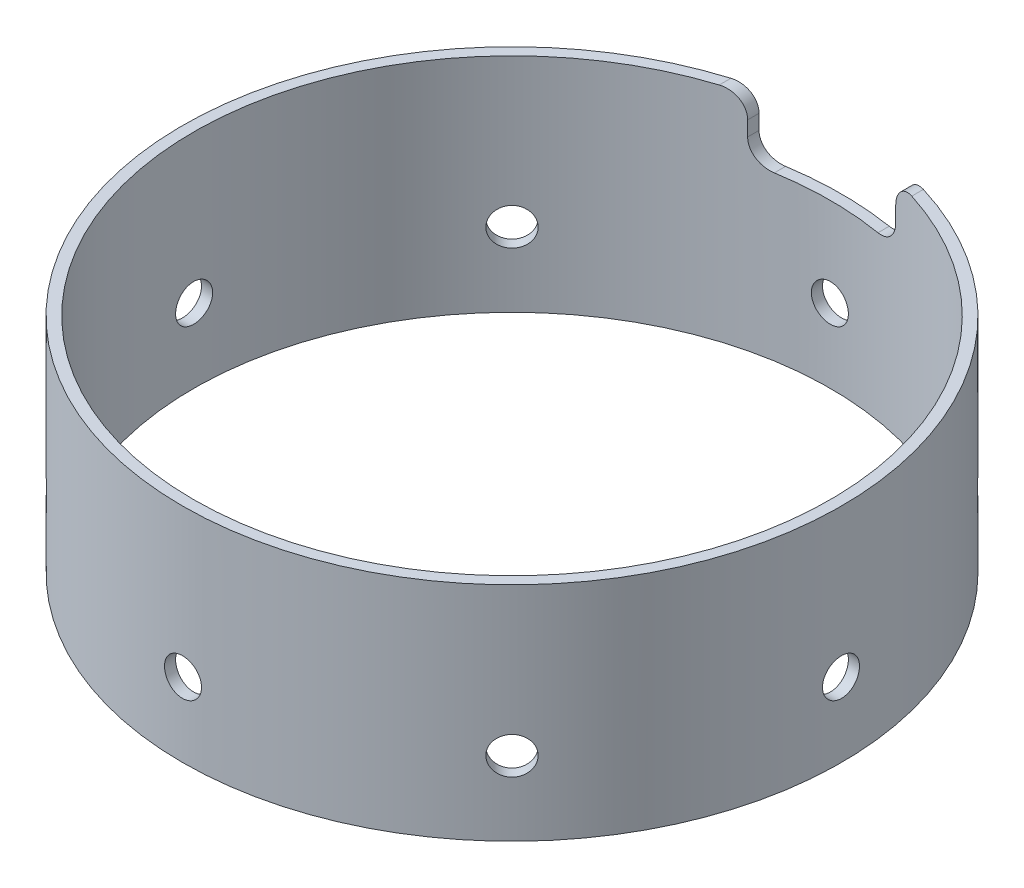
SolidWorks part; units mm, degrees
material "A-Glasfaser"
ref_plane "Ebene vorne" through (0, 0, 0) normal (0, 0, 1) x (1, 0, 0)
ref_plane "Ebene oben" through (0, 0, 0) normal (0, 1, 0) x (1, 0, 0)
ref_plane "Ebene rechts" through (0, 0, 0) normal (1, 0, 0) x (0, 0, -1)
sketch "Skizze1" plane through (0, 0, 0) normal (0, 1, 0) x (1, 0, 0)
  circle A0 centre (0, 0) radius 43
  circle A1 centre (0, 0) radius 44.5
  dimension "D1" = 89
  dimension "D2" = 86
extrude "Aufsatz-Linear austragen1" add sketch "Skizze1" along normal blind 30 contours A0
sketch "Skizze3" plane through (0, 0, 0) normal (0, 0, 1) x (1, 0, 0)
  line L0 (0, 0) -> (0, 30) construction
  line L1 (43, 30) -> (-43, 30) construction
  circle A0 centre (0, 10) radius 2.5
  dimension "D1" = 5
  dimension "D2" = 10
extrude "Schnitt-Linear austragen1" cut sketch "Skizze3" against normal through all
pattern_circular "Kreismuster1" count 8 over 360 about axis through (0, 30, 0) along (0, -1, 0) of "Schnitt-Linear austragen1"
sketch "Skizze4" plane through (0, 0, 0) normal (0, 0, 1) x (1, 0, 0)
  line L0 (-13, 30) -> (13, 30)
  line L1 (44.5, 30) -> (-44.5, 30) construction
  line L2 (10, 27) -> (10, 25)
  line L3 (7, 22) -> (-7, 22)
  line L4 (-10, 25) -> (-10, 27)
  line L5 (0, 22) -> (0, 0) construction
  arc A0 (13, 30) -> (10, 27) centre (13, 27) ccw
  arc A1 (10, 25) -> (7, 22) centre (7, 25) cw
  arc A2 (-7, 22) -> (-10, 25) centre (-7, 25) cw
  arc A3 (-10, 27) -> (-13, 30) centre (-13, 27) ccw
  dimension "D1" = 3
  dimension "D2" = 20
  dimension "D3" = 8
extrude "Schnitt-Linear austragen2" cut sketch "Skizze4" against normal through all
